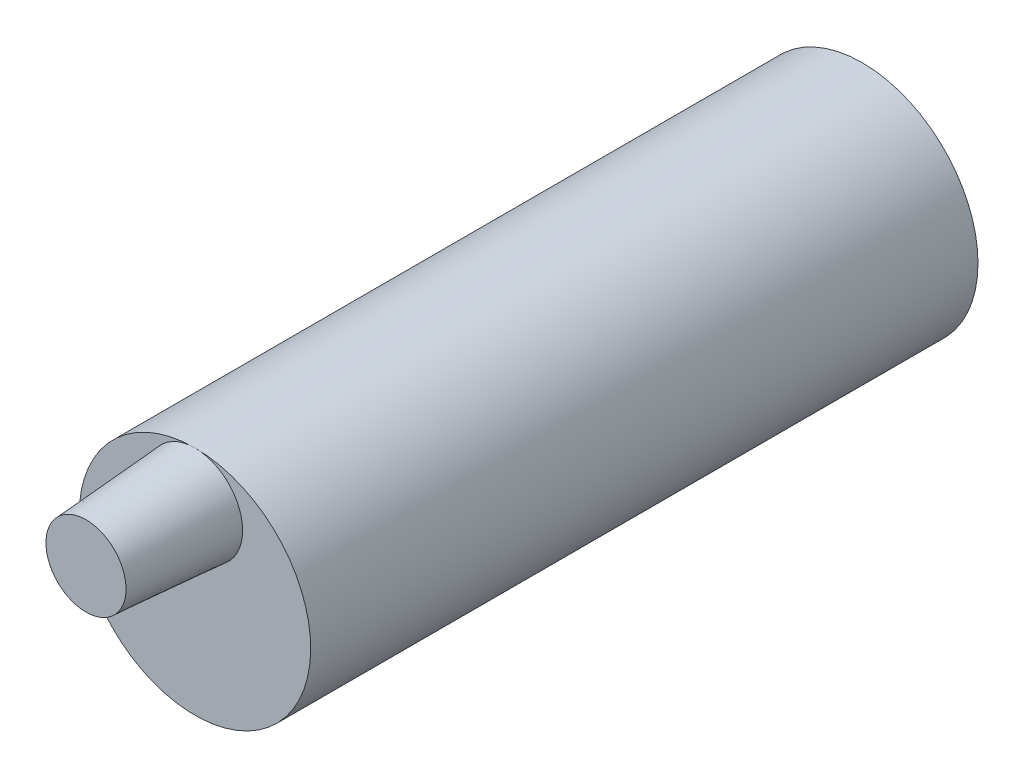
SolidWorks part; units mm, degrees
ref_plane "Front Plane" through (0, 0, 0) normal (0, 0, 1) x (1, 0, 0)
ref_plane "Top Plane" through (0, 0, 0) normal (0, 1, 0) x (1, 0, 0)
ref_plane "Right Plane" through (0, 0, 0) normal (1, 0, 0) x (0, 0, -1)
sketch "Sketch1" plane through (0, 0, 0) normal (0, 0, 1) x (1, 0, 0)
  circle A0 centre (0, 0) radius 8.5
  dimension "D1" = 17
extrude "Boss-Extrude1" add sketch "Sketch1" along normal blind 49
sketch "Sketch2" plane through (0, 0, 49) normal (0, 0, 1) x (1, 0, 0)
  circle A0 centre (0, 5) radius 3.5
  circle A1 centre (0, 0) radius 8.5 construction
  point P2 (0, 4.0735)
  point P3 (0, 4.0476)
  point P6 (0, 0)
  dimension "D1" = 7
extrude "Boss-Extrude2" add sketch "Sketch2" along normal blind 8 draft 4
